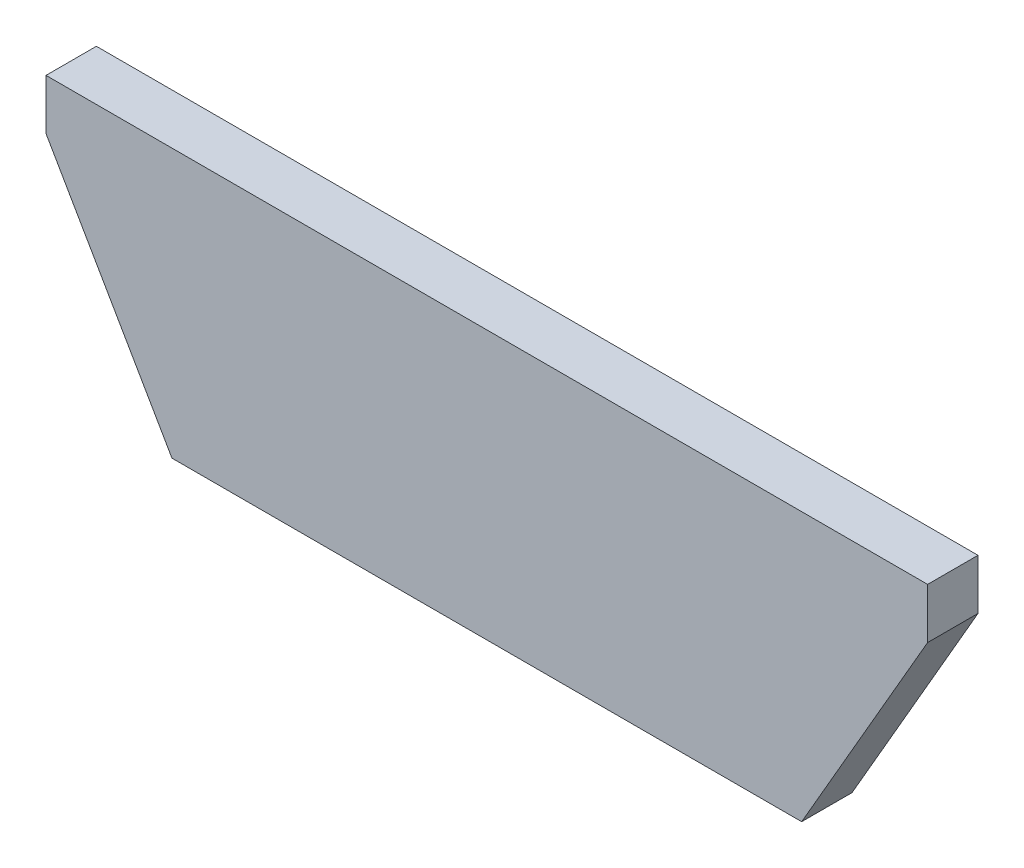
SolidWorks part; units mm, degrees
ref_plane "Front Plane" through (0, 0, 0) normal (0, 0, 1) x (1, 0, 0)
ref_plane "Top Plane" through (0, 0, 0) normal (0, 1, 0) x (1, 0, 0)
ref_plane "Right Plane" through (0, 0, 0) normal (1, 0, 0) x (0, 0, -1)
sketch "Sketch1" plane through (0, 0, 0) normal (0, 0, 1) x (1, 0, 0)
  line L0 (0, 0) -> (63.5, 0)
  line L1 (0, 0) -> (-12.7, 21.997)
  line L2 (63.5, 0) -> (76.2, 21.997)
  line L3 (-12.7, 21.997) -> (-12.7, 27.077)
  line L4 (76.2, 21.997) -> (76.2, 27.077)
  line L5 (-12.7, 27.077) -> (76.2, 27.077)
  dimension "D1" = 63.5
  dimension "D2" = 25.4
  dimension "D3" = 25.4
  dimension "D4" = 120
  dimension "D5" = 120
  dimension "D6" = 5.08
  dimension "D7" = 5.08
extrude "Boss-Extrude1" add sketch "Sketch1" along normal blind 5.08
